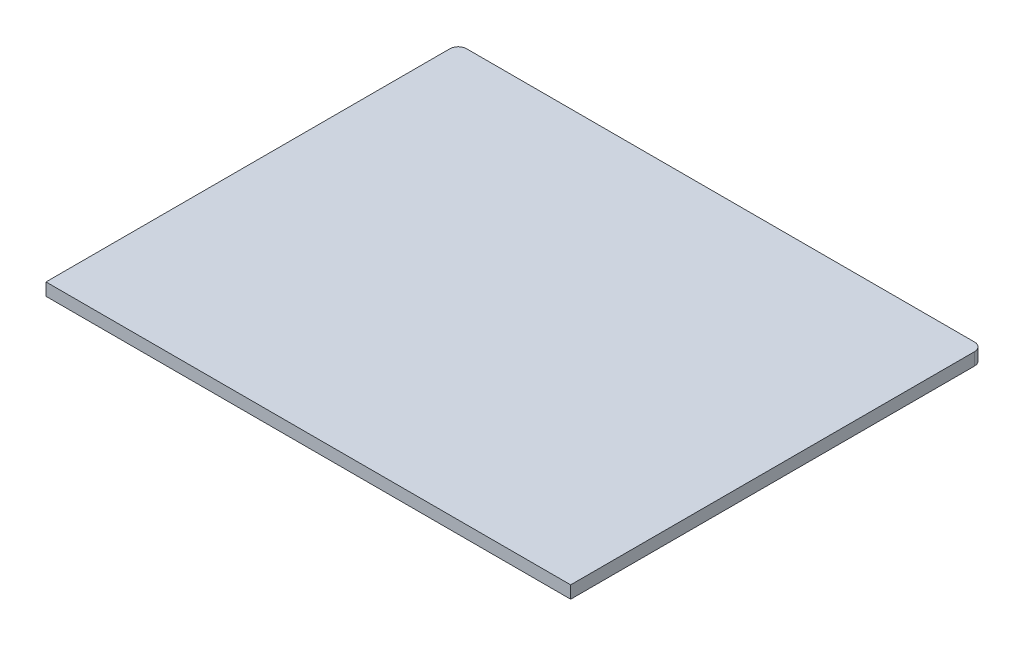
SolidWorks part; units mm, degrees
ref_plane "Front Plane" through (0, 0, 0) normal (0, 0, 1) x (1, 0, 0)
ref_plane "Top Plane" through (0, 0, 0) normal (0, 1, 0) x (1, 0, 0)
ref_plane "Right Plane" through (0, 0, 0) normal (1, 0, 0) x (0, 0, -1)
sketch "Sketch1" plane through (0, 0, 0) normal (0, 1, 0) x (1, 0, 0)
  line L1 (-7.505, 17.9653) -> (55.495, 17.9653)
  line L2 (-7.505, 17.9653) -> (-7.505, -39.0347)
  line L3 (-7.505, -39.0347) -> (55.495, -39.0347)
  line L4 (55.495, 17.9653) -> (55.495, -39.0347)
  dimension "D1" = 57
  dimension "D2" = 63
extrude "Boss-Extrude1" add sketch "Sketch1" along normal blind 1.5
fillet "Fillet1" radius 1 1 edges at (55.495, 0.75, 39.0347)
fillet "Fillet2" radius 1 1 edges at (55.495, 0.75, -17.9653)
fillet "Fillet3" radius 1 2 edges at (-7.505, 0.75, -17.9653) (-7.505, 0.75, 39.0347)
sketch "Sketch3" plane through (0, 1.5, 0) normal (0, 1, 0) x (1, 0, 0)
  line L0 (-7.505, 16.9653) -> (-7.505, -38.0347) construction
  line L1 (55.5527, -39.0347) -> (-7.505, -39.0347)
  line L2 (55.5527, -39.0347) -> (55.5527, -31.5347)
  line L3 (55.5527, -31.5347) -> (-7.505, -31.5347)
  line L4 (-7.505, -39.0347) -> (-7.505, -31.5347)
  dimension "D1" = 7.5
extrude "Cut-Extrude2" cut sketch "Sketch3" against normal blind 10
